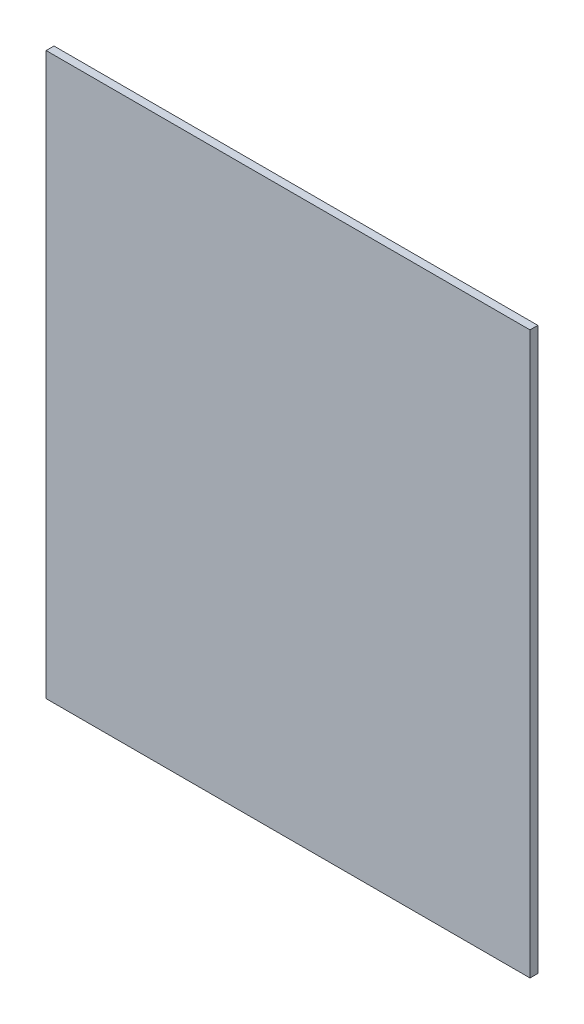
SolidWorks part; units mm, degrees
ref_plane "Plan de face" through (0, 0, 0) normal (0, 0, 1) x (1, 0, 0)
ref_plane "Plan de dessus" through (0, 0, 0) normal (0, 1, 0) x (1, 0, 0)
ref_plane "Plan de droite" through (0, 0, 0) normal (1, 0, 0) x (0, 0, -1)
sketch "Esquisse1" plane through (0, 0, 0) normal (0, 0, 1) x (1, 0, 0)
  line L1 (-106.0717, 231.5471) -> (152.5283, 231.5471)
  line L2 (-106.0717, 231.5471) -> (-106.0717, -68.4529)
  line L3 (-106.0717, -68.4529) -> (152.5283, -68.4529)
  line L4 (152.5283, 231.5471) -> (152.5283, -68.4529)
  dimension "D1" = 258.6
  dimension "D2" = 300
extrude "Boss.-Extru.1" add sketch "Esquisse1" along normal blind 4.2
